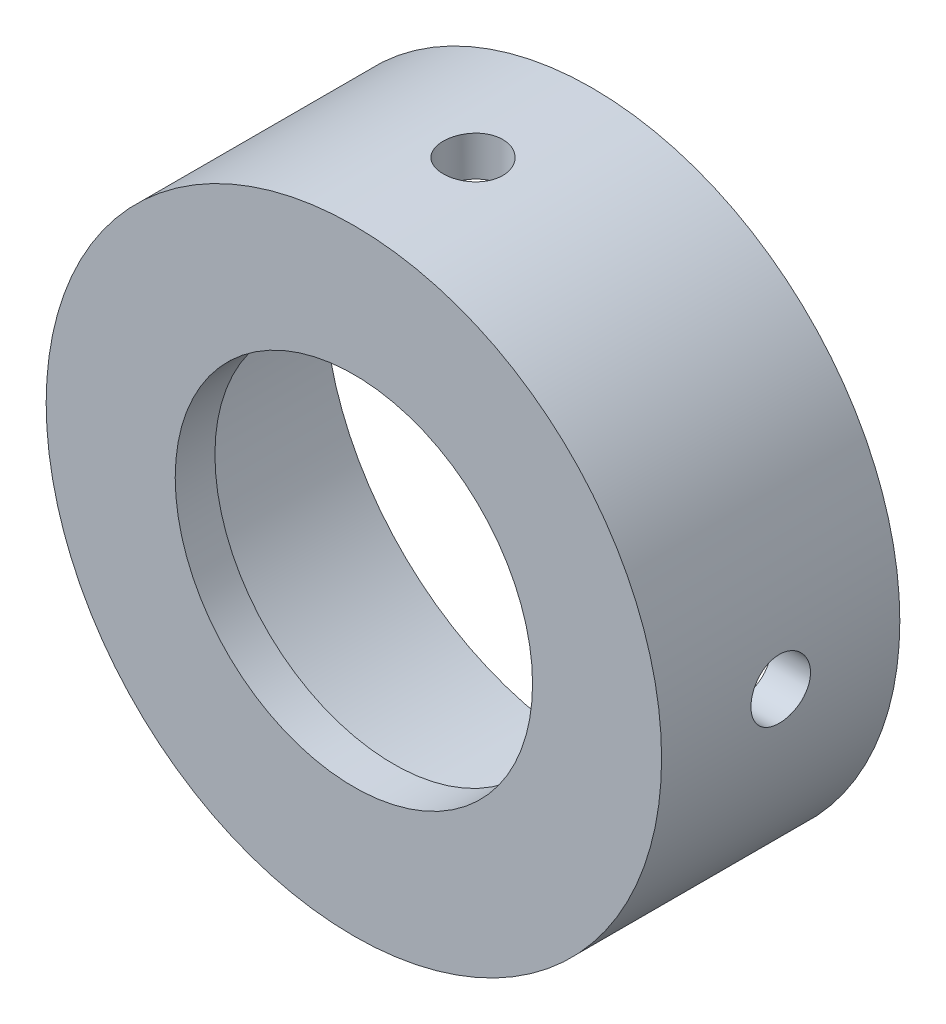
SolidWorks part; units mm, degrees
material "AISI 1035 Acier (SS)"
ref_plane "Plan de face" through (0, 0, 0) normal (0, 0, 1) x (1, 0, 0)
ref_plane "Plan de dessus" through (0, 0, 0) normal (0, 1, 0) x (1, 0, 0)
ref_plane "Plan de droite" through (0, 0, 0) normal (1, 0, 0) x (0, 0, -1)
sketch "Esquisse1" plane through (0, 0, 0) normal (1, 0, 0) x (0, 0, -1)
  line L0 (-6, 0) -> (6, 0) construction
  line L1 (-6, 15.5) -> (6, 15.5)
  line L2 (6, 15.5) -> (6, 13.5)
  line L3 (6, 13.5) -> (-4, 13.5)
  line L4 (-4, 13.5) -> (-4, 9)
  line L5 (-4, 9) -> (-6, 9)
  line L6 (-6, 9) -> (-6, 15.5)
  dimension "D1" = 9
  dimension "D2" = 2
  dimension "D3" = 13.5
  dimension "D4" = 2
  dimension "D5" = 12
revolve "Révolution1" add sketch "Esquisse1" angle 360 about L0
ref_plane "Plan1" through (0, 15.5, 0) normal (0, 1, 0) x (1, 0, 0)
sketch "Esquisse3" plane through (0, 15.5, 0) normal (0, 1, 0) x (1, 0, 0)
  circle A0 centre (0, 0) radius 1.5
  circle A1 centre (0, 0.8704) radius 1.5 construction
  circle A2 centre (0, 0) radius 1.5 construction
  point P4 (0.9899, -2.37)
extrude "Enlèv. mat.-Extru.1" cut sketch "Esquisse3" against normal blind 5
pattern_circular "Répétition circulaire1" count 4 over 360 about axis through (0, 0, 6) along (0, 0, 1) of "Enlèv. mat.-Extru.1"
